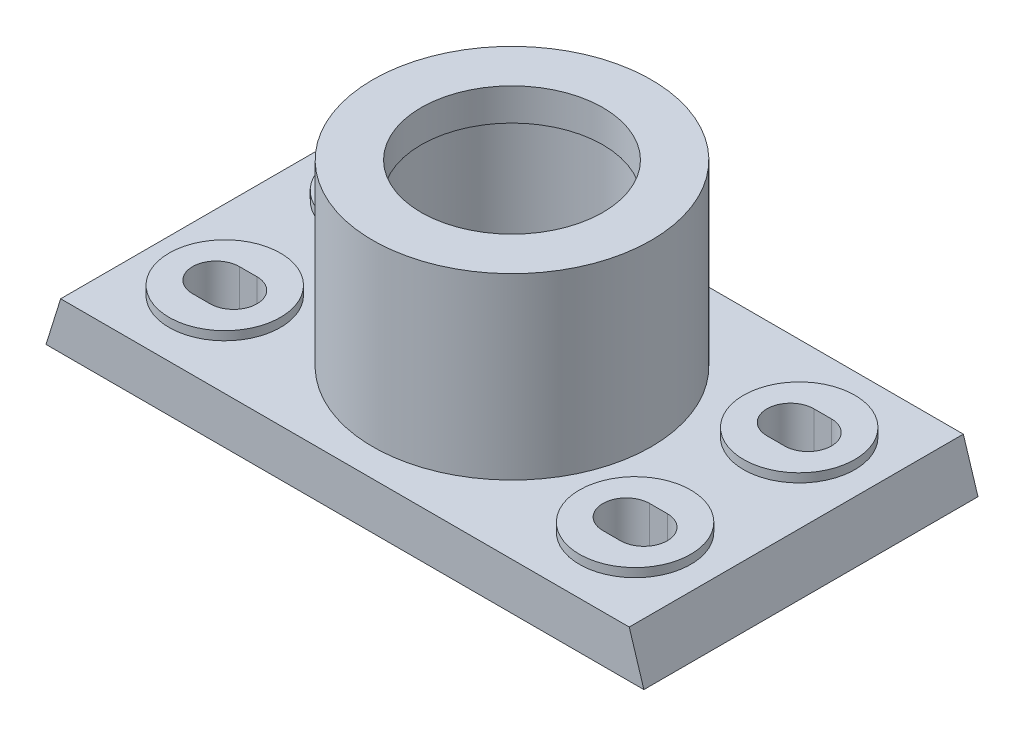
SolidWorks part; units mm, degrees
ref_plane "Front Plane" through (0, 0, 0) normal (0, 0, 1) x (1, 0, 0)
ref_plane "Top Plane" through (0, 0, 0) normal (0, 1, 0) x (1, 0, 0)
ref_plane "Right Plane" through (0, 0, 0) normal (1, 0, 0) x (0, 0, -1)
sketch "Sketch1" plane through (0, 0, 0) normal (0, 0, 1) x (1, 0, 0)
  line L0 (-6.5, 0) -> (6.5, 0)
  line L1 (6.5, 0) -> (6.5, 3)
  line L2 (6.5, 3) -> (92, 3)
  line L3 (92, 3) -> (92, 0)
  line L4 (92, 0) -> (102, 0)
  line L5 (102, 0) -> (97, 16)
  line L6 (97, 16) -> (47.5, 16)
  line L7 (47.5, 16) -> (47.5, 77)
  line L8 (47.5, 77) -> (-47.5, 77)
  line L9 (0, 77) -> (0, 0)
  line L10 (-47.5, 16) -> (-47.5, 77)
  line L11 (-97, 16) -> (-47.5, 16)
  line L12 (-102, 0) -> (-97, 16)
  line L13 (-92, 0) -> (-102, 0)
  line L14 (-92, 3) -> (-92, 0)
  line L15 (-6.5, 3) -> (-92, 3)
  line L16 (-6.5, 0) -> (-6.5, 3)
  line L17 (0, 0) -> (0, 78.6364) construction
  dimension "D1" = 10
  dimension "D2" = 5
  dimension "D3" = 95
  dimension "D4" = 204
  dimension "D5" = 13
  dimension "D6" = 3
  dimension "D7" = 13
  dimension "D8" = 61
extrude "Boss-Extrude1" add sketch "Sketch1" along normal blind 114 contours L16 L0 L9 L8 L10 L11 L12 L13 L14 L15 | L8 L9 L0 L1 L2 L3 L4 L5 L6 L7
sketch "Sketch2" plane through (0, 77, 0) normal (0, 1, 0) x (1, 0, 0)
  circle A1 centre (0, -57) radius 31
  dimension "D1" = 62
extrude "Cut-Extrude1" cut sketch "Sketch2" against normal blind 61
sketch "Sketch3" plane through (0, 77, 0) normal (0, 1, 0) x (1, 0, 0)
  line L0 (-47.5, -57) -> (-47.5, 0)
  line L1 (-47.5, 0) -> (47.5, 0)
  line L2 (47.5, 0) -> (47.5, -114)
  line L3 (47.5, -114) -> (-47.5, -114)
  line L4 (47.5, -114) -> (-47.5, -114) construction
  line L5 (-47.5, -114) -> (-47.5, 0) construction
  line L6 (-47.5, -114) -> (-47.5, -57)
  circle A0 centre (0, -57) radius 47.5
  line M3 (47.5, 0) -> (-47.5, 0)
  line M4 (-47.5, 0) -> (-47.5, -114)
  line M5 (-47.5, -114) -> (47.5, -114)
  line M6 (47.5, -114) -> (47.5, 0)
extrude "Cut-Extrude2" cut sketch "Sketch3" against normal blind 61 contours A0 L2 M3 M4 | A0 M4 M5 M6
ref_plane "Plane1" through (0, 66, 0) normal (0, 1, 0) x (1, 0, 0)
sketch "Sketch5" plane through (0, 66, 0) normal (0, 1, 0) x (1, 0, 0)
  circle A0 centre (0, -57) radius 32.5
  dimension "D1" = 65
extrude "Cut-Extrude3" cut sketch "Sketch5" against normal blind 37
sketch "Sketch6" plane through (0, 16, 0) normal (0, 1, 0) x (1, 0, 0)
  line L0 (-73, -29) -> (-67, -29) construction
  line L1 (-73, -21) -> (-67, -21)
  line L2 (-73, -37) -> (-67, -37)
  line L3 (-97, -114) -> (-97, 0) construction
  line L4 (67, -29) -> (73, -29) construction
  line L5 (67, -21) -> (73, -21)
  line L6 (67, -37) -> (73, -37)
  line L7 (67, -85) -> (73, -85) construction
  line L8 (67, -77) -> (73, -77)
  line L9 (67, -93) -> (73, -93)
  line L10 (-73, -85) -> (-67, -85) construction
  line L11 (-73, -77) -> (-67, -77)
  line L12 (-73, -93) -> (-67, -93)
  arc A0 (-73, -21) -> (-73, -37) centre (-73, -29) ccw
  arc A1 (-67, -37) -> (-67, -21) centre (-67, -29) ccw
  arc A7 (67, -21) -> (67, -37) centre (67, -29) ccw
  arc A8 (73, -37) -> (73, -21) centre (73, -29) ccw
  arc A10 (67, -77) -> (67, -93) centre (67, -85) ccw
  arc A11 (73, -93) -> (73, -77) centre (73, -85) ccw
  arc A13 (-73, -77) -> (-73, -93) centre (-73, -85) ccw
  arc A14 (-67, -93) -> (-67, -77) centre (-67, -85) ccw
  point P2 (-70, -29)
  point P7 (-97, -57)
  point P17 (70, -29)
  point P27 (70, -85)
  point P36 (-70, -85)
  dimension "D2" = 22
  dimension "D1" = 16
  dimension "D3" = 28
  dimension "D4" = 70
  dimension "D6" = 2
  dimension "D7" = 2
extrude "Cut-Extrude4" cut sketch "Sketch6" against normal through all
sketch "Sketch7" plane through (0, 16, 0) normal (0, 1, 0) x (1, 0, 0)
  circle A0 centre (-70, -29) radius 19
  circle A1 centre (70, -29) radius 19
  circle A2 centre (70, -85) radius 19
  circle A3 centre (-70, -85) radius 19
  arc M1 (-73, -93) -> (-73, -77) centre (-73, -85) cw
  line M2 (-73, -77) -> (-67, -77)
  arc M3 (-67, -77) -> (-67, -93) centre (-67, -85) cw
  line M4 (-67, -93) -> (-73, -93)
  arc M5 (67, -93) -> (67, -77) centre (67, -85) cw
  line M6 (67, -77) -> (73, -77)
  arc M7 (73, -77) -> (73, -93) centre (73, -85) cw
  line M8 (73, -93) -> (67, -93)
  arc M9 (67, -37) -> (67, -21) centre (67, -29) cw
  line M10 (67, -21) -> (73, -21)
  arc M11 (73, -21) -> (73, -37) centre (73, -29) cw
  line M12 (73, -37) -> (67, -37)
  arc M13 (-73, -37) -> (-73, -21) centre (-73, -29) cw
  line M14 (-73, -21) -> (-67, -21)
  arc M15 (-67, -21) -> (-67, -37) centre (-67, -29) cw
  line M16 (-67, -37) -> (-73, -37)
  dimension "D1" = 38
  dimension "D2" = 2
  dimension "D3" = 2
extrude "Boss-Extrude3" add sketch "Sketch7" along normal blind 3 contours A0 M16 M13 M14 M15 | A1 M12 M9 M10 M11 | A2 M8 M5 M6 M7 | A3 M4 M1 M2 M3
sketch "Sketch8" plane through (0, 3, 0) normal (0, -1, 0) x (-1, 0, 0)
  line L0 (6.5, 0) -> (92, 0)
  line L1 (92, 0) -> (92, -10)
  line L2 (92, -114) -> (6.5, -114)
  line L3 (6.5, -114) -> (6.5, -104)
  line L4 (6.5, -114) -> (6.5, 0) construction
  line L5 (6.5, -104) -> (92, -104)
  line L7 (92, -10) -> (6.5, -10)
  line L8 (6.5, -10) -> (6.5, 0)
  line L10 (92, -104) -> (92, -114)
  dimension "D1" = 10
  dimension "D2" = 10
extrude "Boss-Extrude4" add sketch "Sketch8" along normal blind 3
sketch "Sketch9" plane through (0, 3, 0) normal (0, -1, 0) x (-1, 0, 0)
  line L0 (-6.5, -114) -> (-92, -114)
  line L1 (-92, -114) -> (-92, -104)
  line L2 (-92, -114) -> (-92, 0) construction
  line L3 (-92, -104) -> (-6.5, -104)
  line L4 (-6.5, -114) -> (-6.5, 0) construction
  line L5 (-6.5, -104) -> (-6.5, -114)
  line L6 (-92, -10) -> (-92, 0)
  line L7 (-92, -114) -> (-92, 0) construction
  line L8 (-92, 0) -> (-6.5, 0)
  line L9 (-6.5, 0) -> (-6.5, -10)
  line L10 (-6.5, -10) -> (-92, -10)
  dimension "D1" = 10
  dimension "D2" = 10
extrude "Boss-Extrude5" add sketch "Sketch9" along normal blind 3
hole_wizard "Ø3.0mm Dowel Hole1" positions "Sketch13" profile "Sketch14" hole size "Ø3.0" standard "ANSI Metric"
sketch "Sketch13" plane through (0, 16, 0) normal (0, 1, 0) x (1, 0, 0)
  line L0 (0, -42.35) -> (0, 42.35) construction
  line L1 (-42.35, 0) -> (42.35, 0) construction
  point P0 (-22, -57)
  dimension "D1" = 22
  dimension "D2" = 57
sketch "Sketch14" plane through (-22, 16, 57) normal (1, 0, 0) x (0, 0, 1)
  line L0 (0, 0) -> (0, 5)
  line L1 (0, 5) -> (1.5, 5)
  line L2 (1.5, 5) -> (1.5, 0)
  line L5 (1.5, 0) -> (0, 0)
  line L10 (0, 5) -> (-1.5, 5) construction
  line L11 (0, -6.35) -> (0, 107.95) construction
  dimension "Hole Dia." = 3
  dimension "Hole Depth" = 5
  dimension "Drill Angle" = 180
